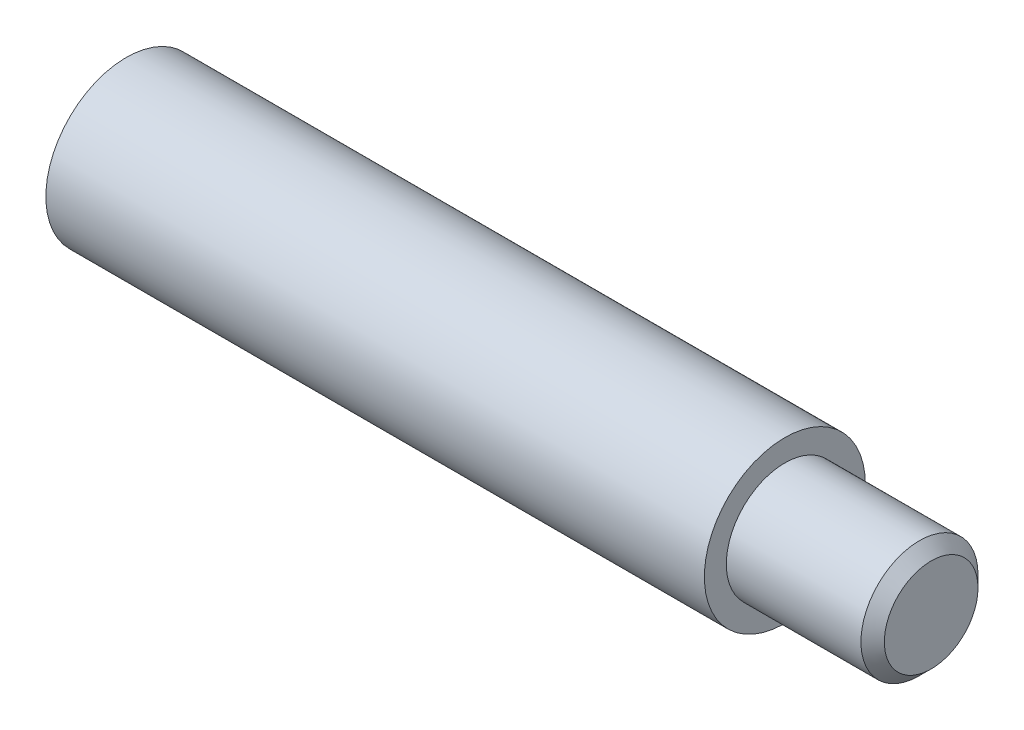
SolidWorks part; units mm, degrees
material "Malleable Cast Iron"
ref_plane "Front Plane" through (0, 0, 0) normal (0, 0, 1) x (1, 0, 0)
ref_plane "Top Plane" through (0, 0, 0) normal (0, 1, 0) x (1, 0, 0)
ref_plane "Right Plane" through (0, 0, 0) normal (1, 0, 0) x (0, 0, -1)
sketch "Sketch1" plane through (0, 0, 0) normal (0, 0, 1) x (1, 0, 0)
  line L0 (-15.5, 2.4585) -> (-14.0228, 0)
  line L1 (-14.0228, 0) -> (27.5, 0)
  line L2 (27.5, 0) -> (27.5, 3.2)
  line L3 (27.5, 3.2) -> (26.7, 4)
  line L4 (26.7, 4) -> (17.5, 4)
  line L5 (17.5, 4) -> (17.5, 5.5)
  line L6 (17.5, 5.5) -> (-27.5, 5.5)
  line L7 (-27.5, 5.5) -> (-27.5, 3.2585)
  line L8 (-27.5, 3.2585) -> (-26.7, 2.4585)
  line L9 (-26.7, 2.4585) -> (-15.5, 2.4585)
  line L10 (-27.5, 0) -> (27.5, 0) construction
revolve "Revolve1" add sketch "Sketch1" angle 360 about L10
